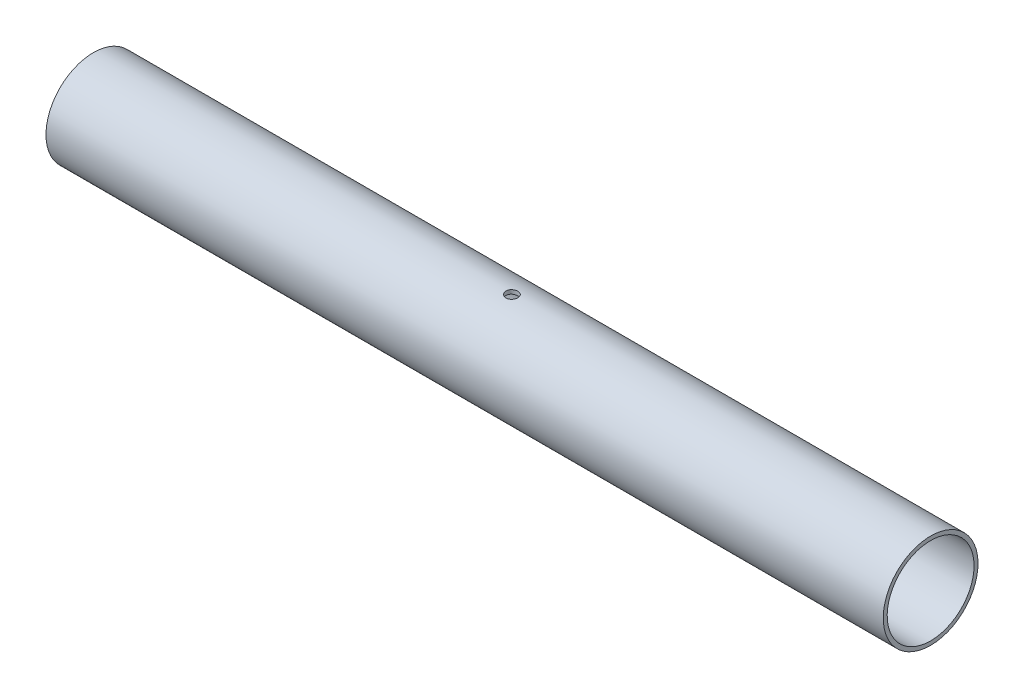
SolidWorks part; units mm, degrees
material "Hexcel AS4C (3000 Filaments)"
ref_plane "Front Plane" through (0, 0, 0) normal (0, 0, 1) x (1, 0, 0)
ref_plane "Top Plane" through (0, 0, 0) normal (0, 1, 0) x (1, 0, 0)
ref_plane "Right Plane" through (0, 0, 0) normal (1, 0, 0) x (0, 0, -1)
sketch "Sketch1" plane through (-15.5279, 0, 0) normal (-1, 0, 0) x (0, 0, 1)
  circle A1 centre (50, 105.8696) radius 11
  circle A2 centre (50, 105.8696) radius 12
  dimension "D2" = 22
  dimension "D1" = 1
extrude "Boss-Extrude1" add sketch "Sketch1" against normal mid plane 212
ref_plane "Plane1" through (0, 117.8696, 0) normal (0, 1, 0) x (1, 0, 0)
sketch "Sketch2" plane through (0, 117.8696, 0) normal (0, 1, 0) x (1, 0, 0)
  line L0 (90.4721, -62) -> (90.4721, -38) construction
  line L1 (-121.5279, -38) -> (-121.5279, -62) construction
  line L2 (90.4721, -62) -> (90.4721, -38) construction
  line L3 (-121.5279, -38) -> (-121.5279, -62) construction
  line L4 (-121.5279, -50) -> (90.4721, -50) construction
  circle A0 centre (-15.5279, -50) radius 1.5
  dimension "D1" = 3
extrude "Cut-Extrude1" cut sketch "Sketch2" against normal through all
equation "\"inner_fuselage_width\"=212"
equation "\"D1@Boss-Extrude1\"=\"inner_fuselage_width\""
